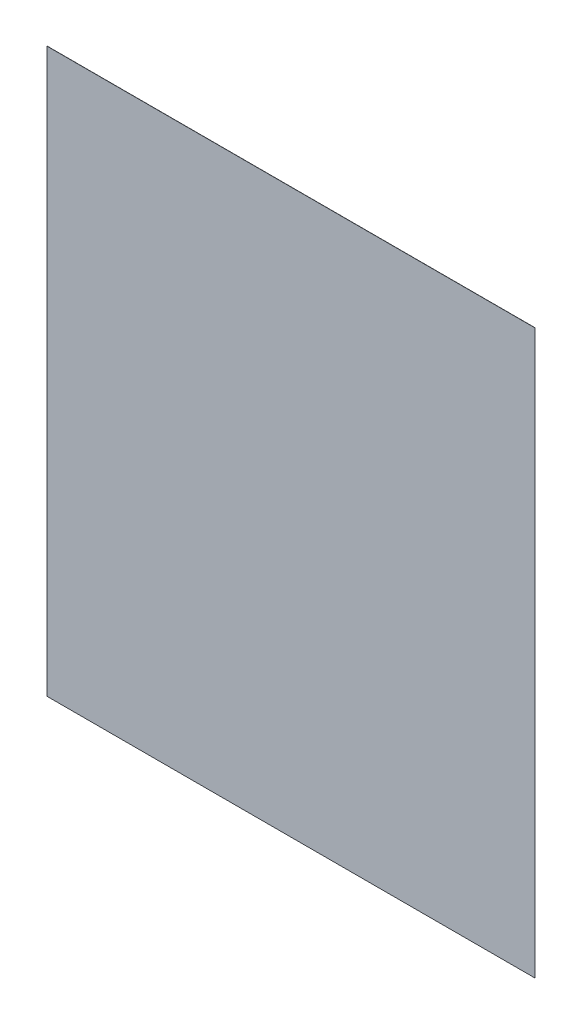
SolidWorks part; units mm, degrees
ref_plane "Спереди" through (0, 0, 0) normal (0, 0, 1) x (1, 0, 0)
ref_plane "Сверху" through (0, 0, 0) normal (0, 1, 0) x (1, 0, 0)
ref_plane "Справа" through (0, 0, 0) normal (1, 0, 0) x (0, 0, -1)
sketch "Эскиз1" plane through (0, 0, 0) normal (0, 0, 1) x (1, 0, 0)
  line L1 (130, -150) -> (-130, -150)
  line L2 (130, -150) -> (130, 150)
  line L3 (130, 150) -> (-130, 150)
  line L4 (-130, -150) -> (-130, 150)
  line L5 (130, -150) -> (-130, 150) construction
  line L6 (130, 150) -> (-130, -150) construction
  point P0 (0, 0)
extrude "Бобышка-Вытянуть1" add sketch "Эскиз1" along normal blind 0.1
